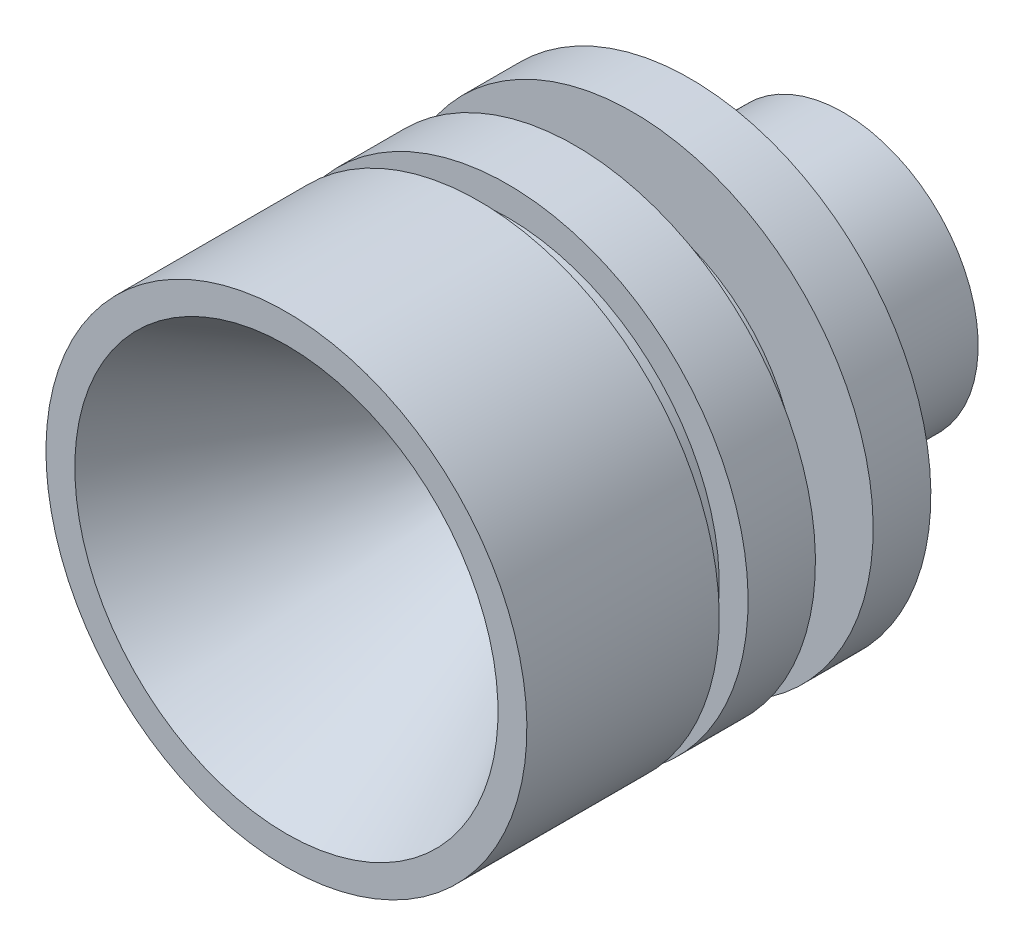
SolidWorks part; units mm, degrees
material "AISI 1035 Acier (SS)"
ref_plane "Plan de face" through (0, 0, 0) normal (0, 0, 1) x (1, 0, 0)
ref_plane "Plan de dessus" through (0, 0, 0) normal (0, 1, 0) x (1, 0, 0)
ref_plane "Plan de droite" through (0, 0, 0) normal (1, 0, 0) x (0, 0, -1)
sketch "Esquisse1" plane through (0, 0, 0) normal (1, 0, 0) x (0, 0, -1)
  line L0 (-14.4796, 0) -> (14.4796, 0) construction
  line L1 (-14.4796, 12.5) -> (-4.4796, 12.5)
  line L3 (14.4796, 4.5) -> (1.5419, 1.75)
  line L4 (-14.4796, 12.5) -> (-14.4796, 11)
  line L5 (-14.4796, 11) -> (1.5419, 1.75)
  line L6 (-4.4796, 12.5) -> (-4.4796, 11)
  line L7 (-4.4796, 11) -> (-2.9796, 11)
  line L8 (-2.9796, 11) -> (-2.9796, 12.5)
  line L9 (0.5204, 12.5) -> (0.5204, 8.5)
  line L10 (0.5204, 8.5) -> (3.5204, 8.5)
  line L11 (3.5204, 8.5) -> (3.5204, 12.5)
  line L12 (-2.9796, 12.5) -> (0.5204, 12.5)
  line L13 (3.5204, 12.5) -> (6.5204, 12.5)
  line L15 (6.5204, 12.5) -> (6.5204, 7)
  line L17 (14.4796, 7) -> (14.4796, 4.5)
  line L18 (6.5204, 7) -> (14.4796, 7)
  point P16 (9.9652, 4.5)
  dimension "D2" = 12.5
  dimension "D3" = 1.75
  dimension "D4" = 4.5
  dimension "D5" = 30
  dimension "D6" = 12
  dimension "D7" = 10
  dimension "D8" = 1.5
  dimension "D9" = 1.5
  dimension "D10" = 4
  dimension "D11" = 3
  dimension "D12" = 15
  dimension "D13" = 11
  dimension "D14" = 3
  dimension "D15" = 2.5
revolve "Révolution1" add sketch "Esquisse1" angle 360 about L0
fillet "Congé1" [suppressed] radius 1
chamfer "Chanfrein1" [suppressed] distance 1 angle 30
